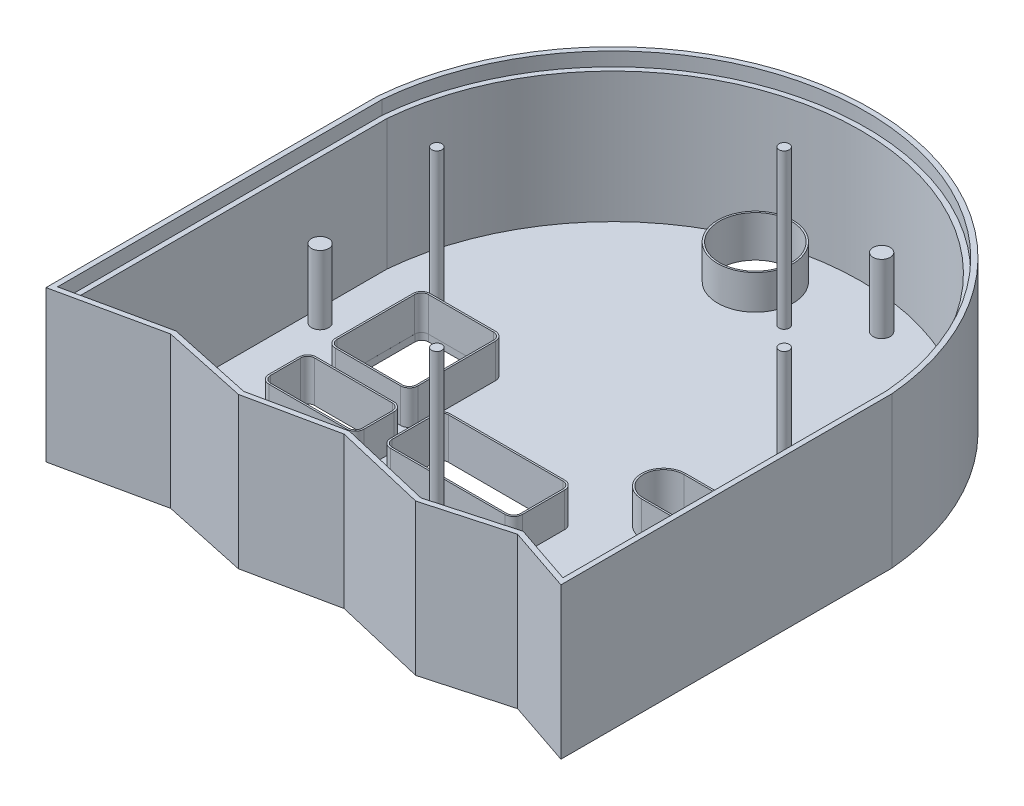
SolidWorks part; units mm, degrees
ref_plane "Front Plane" through (0, 0, 0) normal (0, 0, 1) x (1, 0, 0)
ref_plane "Top Plane" through (0, 0, 0) normal (0, 1, 0) x (1, 0, 0)
ref_plane "Right Plane" through (0, 0, 0) normal (1, 0, 0) x (0, 0, -1)
sketch "Sketch2" plane through (0, 0, 0) normal (0, 1, 0) x (1, 0, 0)
  line L0 (0, 0) -> (0, 50.59) construction
  line L1 (0, 0) -> (-50.59, 0) construction
  line L2 (0, 0) -> (0, -50.59) construction
  line L3 (0, 0) -> (50.59, 0) construction
  circle A0 centre (0, 50.59) radius 1.5
  circle A1 centre (0, -50.59) radius 1.5
  circle A2 centre (-50.59, 0) radius 1.5
  circle A3 centre (50.59, 0) radius 1.5
  dimension "D5" = 3
  dimension "D6" = 3
extrude "Boss-Extrude1" add sketch "Sketch2" along normal blind 47
sketch "Sketch3" plane through (0, 0, 0) normal (0, 1, 0) x (1, 0, 0)
  line L0 (-61.4941, 0) -> (61.4941, 0) construction
  line L1 (0, 50.59) -> (0, 75.59) construction
  line L2 (-75, 0) -> (75, 0) construction
  line L3 (-75, -83) -> (-75, -89.4475)
  line L5 (-75, 7) -> (-75, -83)
  line L7 (75, 7) -> (75, -83)
  line L8 (-75, -89.4475) -> (-45.1254, -83)
  line L9 (75, -83) -> (75, -89.4475)
  line L10 (75, -89.4475) -> (55.9292, -83)
  line L11 (55.9292, -83) -> (32.7122, -89.4475)
  line L12 (32.7122, -89.4475) -> (5.4019, -83)
  line L13 (5.4019, -83) -> (-20.0295, -88.3739)
  line L14 (-20.0295, -88.3739) -> (-45.1254, -83)
  arc A1 (-75, 7) -> (75, 7) centre (0, 0.6131) cw
  point P3 (0, 0)
  point P9 (0, 0)
  dimension "D1" = 25
  dimension "D2" = 90
extrude "Boss-Extrude3" add sketch "Sketch3" along normal blind 2
sketch "Sketch4" plane through (0, 2, 0) normal (0, 1, 0) x (1, 0, 0)
  line L0 (-0.203, 50.5015) -> (-15.203, 50.5015) construction
  line L6 (-15.203, 50.5015) -> (-15.203, 57.4015) construction
  line L20 (-30.5269, -3.4521) -> (-49.5464, -3.4521)
  line L26 (-28.5269, -5.4521) -> (-28.5269, -21.6404)
  line L27 (-50.1469, -36.0953) -> (-27.4709, -36.0953)
  line L28 (38.06, -4.6382) -> (38.06, -16.6082) construction
  line L32 (-25.4709, -38.0953) -> (-25.4709, -46.8542)
  line L42 (-27.4709, -48.8542) -> (-50.1469, -48.8542)
  line L45 (-52.1469, -46.8542) -> (-52.1469, -38.0953)
  line L52 (33.06, -17.5981) -> (43.06, -17.5981) construction
  line L53 (33.06, -11.6859) -> (43.06, -11.6859)
  line L55 (33.06, -23.5104) -> (43.06, -23.5104)
  line L58 (-18.2979, -32.9201) -> (-18.2979, -45.3138)
  line L61 (19.1213, -32.9614) -> (19.1213, -45.3138)
  line L62 (-28.5269, -21.6404) -> (-28.5269, -28.0374)
  line L63 (17.1238, -30.9614) -> (-16.2955, -30.9201)
  line L65 (-16.2979, -47.3138) -> (17.1213, -47.3138)
  line L67 (-30.5269, -30.0374) -> (-49.5464, -30.0374)
  line L71 (-51.5464, -28.0374) -> (-51.5464, -5.4521)
  circle A1 centre (-15.203, 57.4015) radius 10.46
  arc A3 (33.06, -11.6859) -> (33.06, -23.5104) centre (33.06, -17.5981) ccw
  arc A4 (43.06, -23.5104) -> (43.06, -11.6859) centre (43.06, -17.5981) ccw
  arc A5 (19.1213, -32.9614) -> (17.1238, -30.9614) centre (17.1213, -32.9614) ccw
  arc A6 (17.1213, -47.3138) -> (19.1213, -45.3138) centre (17.1213, -45.3138) ccw
  arc A7 (-18.2979, -45.3138) -> (-16.2979, -47.3138) centre (-16.2979, -45.3138) ccw
  arc A8 (-18.2979, -32.9201) -> (-16.2955, -30.9201) centre (-16.2979, -32.9201) cw
  arc A9 (-27.4709, -48.8542) -> (-25.4709, -46.8542) centre (-27.4709, -46.8542) ccw
  arc A10 (-27.4709, -36.0953) -> (-25.4709, -38.0953) centre (-27.4709, -38.0953) cw
  arc A11 (-50.1469, -48.8542) -> (-52.1469, -46.8542) centre (-50.1469, -46.8542) cw
  arc A12 (-52.1469, -38.0953) -> (-50.1469, -36.0953) centre (-50.1469, -38.0953) cw
  arc A13 (-49.5464, -30.0374) -> (-51.5464, -28.0374) centre (-49.5464, -28.0374) cw
  arc A14 (-49.5464, -3.4521) -> (-51.5464, -5.4521) centre (-49.5464, -5.4521) ccw
  arc A15 (-28.5269, -28.0374) -> (-30.5269, -30.0374) centre (-30.5269, -28.0374) cw
  arc A16 (-28.5269, -5.4521) -> (-30.5269, -3.4521) centre (-30.5269, -5.4521) ccw
  point P8 (38.06, -17.5981)
  dimension "D3" = 15
  dimension "D5" = 20.92
  dimension "D7" = 2
  dimension "D8" = 2
  dimension "D9" = 2
  dimension "D1" = 10
  dimension "D2" = 11.97
  dimension "D4" = 6.9
extrude "Cut-Extrude1" cut sketch "Sketch4" against normal through all
sketch "Sketch5" plane through (0, 2, 0) normal (0, 1, 0) x (1, 0, 0)
  line L0 (-75, -89.4475) -> (-45.1254, -83)
  line L4 (5.4019, -83) -> (32.7122, -89.4475)
  line L5 (32.7122, -89.4475) -> (55.9292, -83)
  line L6 (55.9292, -83) -> (75, -89.4475) construction
  line L7 (32.7122, -89.4475) -> (55.9292, -83) construction
  line L8 (55.9292, -83) -> (75, -89.4475)
  line L9 (75, -89.4475) -> (75, 7)
  line L11 (-75, 7) -> (-75, -89.4475) construction
  line L12 (-75, 7) -> (-75, -89.4475)
  line L13 (-45.1254, -83) -> (-20.0295, -88.3739)
  line L14 (-20.0295, -88.3739) -> (5.4019, -83)
  line L15 (-72, -85.731) -> (-45.1279, -79.9315)
  line L16 (-45.1279, -79.9315) -> (-20.0253, -85.3068)
  line L17 (-20.0253, -85.3068) -> (5.4382, -79.9261)
  line L18 (5.4382, -79.9261) -> (32.6517, -86.3508)
  line L19 (32.6517, -86.3508) -> (56.0158, -79.8624)
  line L20 (56.0158, -79.8624) -> (72, -85.2665)
  line L21 (72, -85.2665) -> (72, 6.8712)
  line L22 (-72, 6.8712) -> (-72, -85.731)
  arc A0 (75, 7) -> (-75, 7) centre (0, 0.6131) ccw construction
  arc A1 (-75, 7) -> (75, 7) centre (0, 0.6131) cw
  arc A2 (-72, 6.8712) -> (72, 6.8712) centre (0, 0.6131) cw
  dimension "D1" = 3
extrude "Boss-Extrude4" add sketch "Sketch5" along normal blind 42
sketch "Sketch6" plane through (0, 2, 0) normal (0, 1, 0) x (1, 0, 0)
  circle A0 centre (60.6468, -72.7946) radius 2.5
  circle A1 centre (-68.1861, -16.4048) radius 2.5
  circle A2 centre (15.8431, 63.1498) radius 2.5
  dimension "D1" = 5
extrude "Boss-Extrude5" add sketch "Sketch6" along normal blind 20
sketch "Sketch8" plane through (0, 44, 0) normal (0, 1, 0) x (1, 0, 0)
  line L8 (56.0158, -79.8624) -> (72, -85.2665) construction
  line L9 (32.6517, -86.3508) -> (56.0158, -79.8624) construction
  line L10 (5.4382, -79.9261) -> (32.6517, -86.3508) construction
  line L11 (-20.0253, -85.3068) -> (5.4382, -79.9261) construction
  line L12 (-45.1279, -79.9315) -> (-20.0253, -85.3068) construction
  line L13 (-72, -85.731) -> (-45.1279, -79.9315) construction
  line L14 (-72, 6.8712) -> (-72, -85.731) construction
  line L15 (72, -85.2665) -> (72, 6.8712) construction
  line L16 (-73.5, -87.5893) -> (-45.1266, -81.4657)
  line L17 (-45.1266, -81.4657) -> (-20.0274, -86.8404)
  line L18 (-20.0274, -86.8404) -> (5.4201, -81.463)
  line L19 (5.4201, -81.463) -> (32.682, -87.8992)
  line L20 (32.682, -87.8992) -> (55.9725, -81.4312)
  line L21 (55.9725, -81.4312) -> (73.5, -87.357)
  line L22 (73.5, -87.357) -> (73.5, 6.9359)
  line L23 (-73.5, 6.9359) -> (-73.5, -87.5893)
  line L24 (-73.5, -87.5893) -> (-45.1266, -81.4657)
  line L25 (-45.1266, -81.4657) -> (-20.0274, -86.8404)
  line L26 (-20.0274, -86.8404) -> (5.4201, -81.463)
  line L27 (5.4201, -81.463) -> (32.682, -87.8992)
  line L28 (32.682, -87.8992) -> (55.9725, -81.4312)
  line L29 (55.9725, -81.4312) -> (73.5, -87.357)
  line L30 (73.5, -87.357) -> (73.5, 6.9359)
  line L31 (-73.5, 6.9359) -> (-73.5, -87.5893)
  line L32 (56.0158, -79.8624) -> (72, -85.2665)
  line L33 (32.6517, -86.3508) -> (56.0158, -79.8624)
  line L34 (5.4382, -79.9261) -> (32.6517, -86.3508)
  line L35 (-20.0253, -85.3068) -> (5.4382, -79.9261)
  line L36 (-45.1279, -79.9315) -> (-20.0253, -85.3068)
  line L37 (-72, -85.731) -> (-45.1279, -79.9315)
  line L38 (-72, 6.8712) -> (-72, -85.731)
  line L39 (72, -85.2665) -> (72, 6.8712)
  arc A1 (72, 6.8712) -> (-72, 6.8712) centre (0, 0.6131) ccw construction
  arc A2 (73.5, 6.9359) -> (-73.5, 6.9359) centre (0, 0.6131) ccw
  arc A3 (73.5, 6.9359) -> (-73.5, 6.9359) centre (0, 0.6131) ccw
  arc A4 (72, 6.8712) -> (-72, 6.8712) centre (0, 0.6131) ccw
  dimension "D1" = 1.5
extrude "Cut-Extrude3" cut sketch "Sketch8" against normal blind 4
sketch "Sketch9" plane through (0, 2, 0) normal (0, 1, 0) x (1, 0, 0)
  circle A0 centre (32.5708, -77.2265) radius 6.5
  dimension "D1" = 13
extrude "Cut-Extrude4" cut sketch "Sketch9" against normal through all
sketch "Sketch11" plane through (0, 2, 0) normal (0, 1, 0) x (1, 0, 0)
  line L1 (-50.1469, -48.8542) -> (-27.4709, -48.8542) construction
  line L3 (-52.1469, -38.0953) -> (-52.1469, -46.8542) construction
  line L4 (-27.4709, -36.0953) -> (-50.1469, -36.0953) construction
  line L5 (-25.4709, -46.8542) -> (-25.4709, -38.0953) construction
  line L6 (-18.2979, -32.9201) -> (-18.2979, -45.3138) construction
  line L7 (19.1213, -45.3138) -> (19.1213, -32.9614) construction
  line L8 (-16.2979, -47.3138) -> (17.1213, -47.3138) construction
  line L9 (17.1238, -30.9614) -> (-16.2955, -30.9201) construction
  line L10 (33.06, -23.5104) -> (43.06, -23.5104) construction
  line L11 (43.06, -11.6859) -> (33.06, -11.6859) construction
  line L12 (-50.1469, -48.8542) -> (-27.4709, -48.8542)
  line L13 (-52.1469, -38.0953) -> (-52.1469, -46.8542)
  line L24 (-49.5509, -30.0786) -> (-30.5314, -30.0786)
  line L25 (-28.5314, -28.0786) -> (-28.5314, -5.4933)
  line L26 (-51.5509, -5.4933) -> (-51.5509, -28.0786)
  line L27 (-30.5314, -3.4933) -> (-49.5509, -3.4933)
  line L38 (-49.5509, -30.5786) -> (-30.5314, -30.5786)
  line L39 (-28.0314, -28.0786) -> (-28.0314, -5.4933)
  line L40 (-30.5314, -2.9933) -> (-49.5509, -2.9933)
  line L41 (-52.0509, -5.4933) -> (-52.0509, -28.0786)
  line L42 (-27.4709, -36.0953) -> (-50.1469, -36.0953)
  line L43 (-25.4709, -46.8542) -> (-25.4709, -38.0953)
  line L44 (-18.2979, -32.9201) -> (-18.2979, -45.3138)
  line L45 (19.1213, -45.3138) -> (19.1213, -32.9614)
  line L46 (-16.2979, -47.3138) -> (17.1213, -47.3138)
  line L47 (17.1238, -30.9614) -> (-16.2955, -30.9201)
  line L48 (33.06, -23.5104) -> (43.06, -23.5104)
  line L49 (43.06, -11.6859) -> (33.06, -11.6859)
  line L50 (-50.1469, -49.3542) -> (-27.4709, -49.3542)
  line L51 (-24.9709, -46.8542) -> (-24.9709, -38.0953)
  line L52 (-27.4709, -35.5953) -> (-50.1469, -35.5953)
  line L53 (-52.6469, -38.0953) -> (-52.6469, -46.8542)
  line L54 (-18.7979, -32.9201) -> (-18.7979, -45.3138)
  line L55 (-16.2979, -47.8138) -> (17.1213, -47.8138)
  line L56 (19.6213, -45.3138) -> (19.6213, -32.9614)
  line L57 (17.1244, -30.4614) -> (-16.2948, -30.4201)
  line L58 (33.06, -24.0104) -> (43.06, -24.0104)
  line L59 (43.06, -11.1859) -> (33.06, -11.1859)
  circle A0 centre (-15.203, 57.4015) radius 10.46 construction
  arc A7 (-27.4709, -48.8542) -> (-25.4709, -46.8542) centre (-27.4709, -46.8542) ccw construction
  arc A8 (-52.1469, -46.8542) -> (-50.1469, -48.8542) centre (-50.1469, -46.8542) ccw construction
  arc A9 (-50.1469, -36.0953) -> (-52.1469, -38.0953) centre (-50.1469, -38.0953) ccw construction
  arc A10 (-25.4709, -38.0953) -> (-27.4709, -36.0953) centre (-27.4709, -38.0953) ccw construction
  arc A11 (-18.2979, -45.3138) -> (-16.2979, -47.3138) centre (-16.2979, -45.3138) ccw construction
  arc A12 (17.1213, -47.3138) -> (19.1213, -45.3138) centre (17.1213, -45.3138) ccw construction
  arc A13 (19.1213, -32.9614) -> (17.1238, -30.9614) centre (17.1213, -32.9614) ccw construction
  arc A14 (-16.2955, -30.9201) -> (-18.2979, -32.9201) centre (-16.2979, -32.9201) ccw construction
  circle A15 centre (-15.203, 57.4015) radius 10.46
  arc A26 (-51.5509, -28.0786) -> (-49.5509, -30.0786) centre (-49.5509, -28.0786) ccw
  arc A27 (-30.5314, -30.0786) -> (-28.5314, -28.0786) centre (-30.5314, -28.0786) ccw
  arc A28 (-49.5509, -3.4933) -> (-51.5509, -5.4933) centre (-49.5509, -5.4933) ccw
  arc A29 (-28.5314, -5.4933) -> (-30.5314, -3.4933) centre (-30.5314, -5.4933) ccw
  arc A40 (-30.5314, -30.5786) -> (-28.0314, -28.0786) centre (-30.5314, -28.0786) ccw
  arc A41 (-28.0314, -5.4933) -> (-30.5314, -2.9933) centre (-30.5314, -5.4933) ccw
  arc A42 (-49.5509, -2.9933) -> (-52.0509, -5.4933) centre (-49.5509, -5.4933) ccw
  arc A43 (-52.0509, -28.0786) -> (-49.5509, -30.5786) centre (-49.5509, -28.0786) ccw
  circle A44 centre (-15.203, 57.4015) radius 10.96
  arc A45 (33.06, -11.6859) -> (33.06, -23.5104) centre (33.06, -17.5981) ccw construction
  arc A46 (43.06, -23.5104) -> (43.06, -11.6859) centre (43.06, -17.5981) ccw construction
  arc A47 (-27.4709, -48.8542) -> (-25.4709, -46.8542) centre (-27.4709, -46.8542) ccw
  arc A48 (-52.1469, -46.8542) -> (-50.1469, -48.8542) centre (-50.1469, -46.8542) ccw
  arc A49 (-50.1469, -36.0953) -> (-52.1469, -38.0953) centre (-50.1469, -38.0953) ccw
  arc A50 (-25.4709, -38.0953) -> (-27.4709, -36.0953) centre (-27.4709, -38.0953) ccw
  arc A51 (-18.2979, -45.3138) -> (-16.2979, -47.3138) centre (-16.2979, -45.3138) ccw
  arc A52 (17.1213, -47.3138) -> (19.1213, -45.3138) centre (17.1213, -45.3138) ccw
  arc A53 (19.1213, -32.9614) -> (17.1238, -30.9614) centre (17.1213, -32.9614) ccw
  arc A54 (-16.2955, -30.9201) -> (-18.2979, -32.9201) centre (-16.2979, -32.9201) ccw
  arc A55 (33.06, -11.6859) -> (33.06, -23.5104) centre (33.06, -17.5981) ccw
  arc A56 (43.06, -23.5104) -> (43.06, -11.6859) centre (43.06, -17.5981) ccw
  arc A57 (-27.4709, -49.3542) -> (-24.9709, -46.8542) centre (-27.4709, -46.8542) ccw
  arc A58 (-24.9709, -38.0953) -> (-27.4709, -35.5953) centre (-27.4709, -38.0953) ccw
  arc A59 (-50.1469, -35.5953) -> (-52.6469, -38.0953) centre (-50.1469, -38.0953) ccw
  arc A60 (-52.6469, -46.8542) -> (-50.1469, -49.3542) centre (-50.1469, -46.8542) ccw
  arc A61 (-18.7979, -45.3138) -> (-16.2979, -47.8138) centre (-16.2979, -45.3138) ccw
  arc A62 (17.1213, -47.8138) -> (19.6213, -45.3138) centre (17.1213, -45.3138) ccw
  arc A63 (19.6213, -32.9614) -> (17.1244, -30.4614) centre (17.1213, -32.9614) ccw
  arc A64 (-16.2948, -30.4201) -> (-18.7979, -32.9201) centre (-16.2979, -32.9201) ccw
  arc A65 (43.06, -24.0104) -> (43.06, -11.1859) centre (43.06, -17.5981) ccw
  arc A66 (33.06, -11.1859) -> (33.06, -24.0104) centre (33.06, -17.5981) ccw
  dimension "D1" = 0.5
extrude "Boss-Extrude9" add sketch "Sketch11" along normal blind 10
